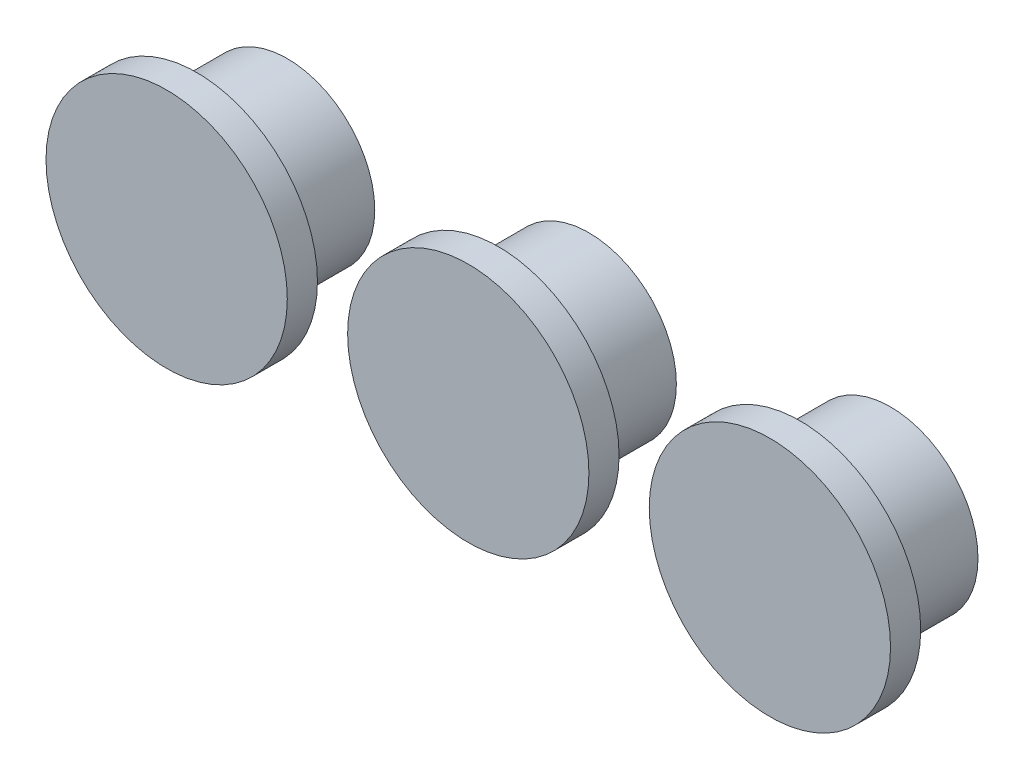
SolidWorks part; units mm, degrees
ref_plane "Plan de face" through (0, 0, 0) normal (0, 0, 1) x (1, 0, 0)
ref_plane "Plan de dessus" through (0, 0, 0) normal (0, 1, 0) x (1, 0, 0)
ref_plane "Plan de droite" through (0, 0, 0) normal (1, 0, 0) x (0, 0, -1)
sketch "Esquisse1" plane through (0, 0, 0) normal (0, 0, 1) x (1, 0, 0)
  circle A0 centre (0, 0) radius 2.9
extrude "Boss.-Extru.1" add sketch "Esquisse1" along normal blind 3
sketch "Esquisse2" plane through (0, 0, 3) normal (0, 0, 1) x (1, 0, 0)
  circle A0 centre (0, 0) radius 4
extrude "Boss.-Extru.2" add sketch "Esquisse2" along normal blind 1
sketch "Esquisse3" plane through (0, 0, 4) normal (0, 0, 1) x (1, 0, 0)
  line L0 (0, 0) -> (19.334, 0) construction
pattern_linear "Répétition linéaire2" count 3 spacing 10 along (-1, 0, 0) of bodies 102
sketch "Esquisse4" plane through (0, 0, 0) normal (0, 0, -1) x (-1, 0, 0)
  line L1 (8.442, 1.5583) -> (11.442, 1.5583)
  line L2 (8.442, 1.5583) -> (8.442, -1.4417)
  line L3 (8.442, -1.4417) -> (11.442, -1.4417)
  line L4 (11.442, 1.5583) -> (11.442, -1.4417)
  text T0 "+\r\n" font "Verdana" height in points 20
  text T1 "-" font "Verdana" height in points 20
  point P2 (12.1602, -1.9348)
  point P7 (11.5109, -1.3213)
  point P8 (8.442, -1.4417)
  point P10 (0, 0)
extrude "Boss.-Extru.3" add sketch "Esquisse4" along normal blind 0.5
